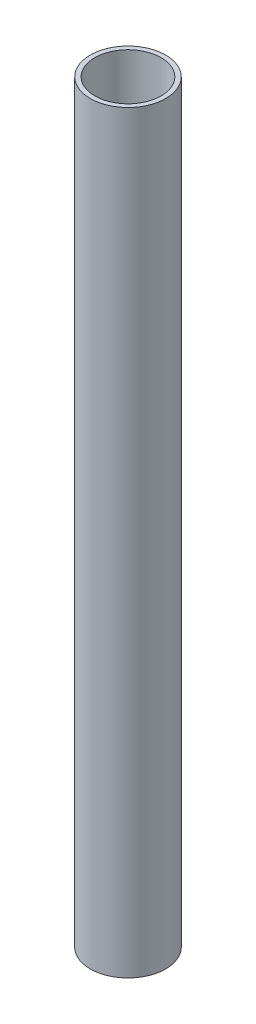
SolidWorks part; units mm, degrees
ref_plane "Front Plane" through (0, 0, 0) normal (0, 0, 1) x (1, 0, 0)
ref_plane "Top Plane" through (0, 0, 0) normal (0, 1, 0) x (1, 0, 0)
ref_plane "Right Plane" through (0, 0, 0) normal (1, 0, 0) x (0, 0, -1)
sketch "Sketch1" plane through (0, 0, 0) normal (0, 1, 0) x (1, 0, 0)
  circle A0 centre (0, 0) radius 12.7
  circle A1 centre (0, 0) radius 11.176
  dimension "D1" = 25.4
  dimension "D2" = 22.352
extrude "Boss-Extrude1" add sketch "Sketch1" along normal blind 254
